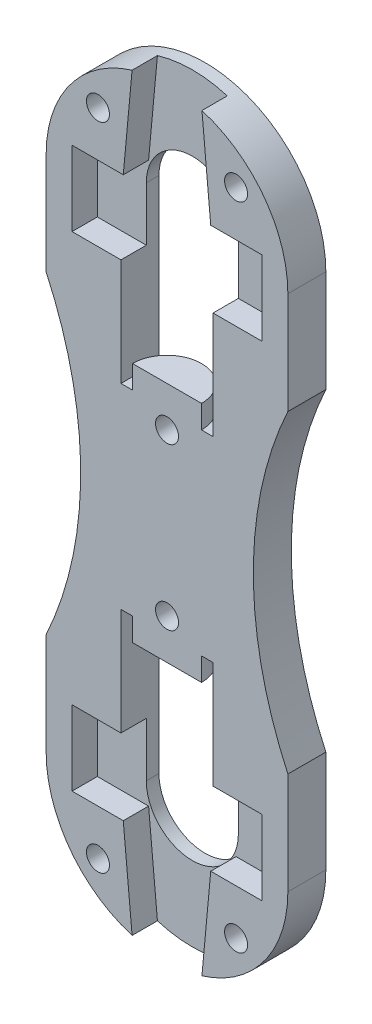
SolidWorks part; units mm, degrees
ref_plane "前视基准面" through (0, 0, 0) normal (0, 0, 1) x (1, 0, 0)
ref_plane "上视基准面" through (0, 0, 0) normal (0, 1, 0) x (1, 0, 0)
ref_plane "右视基准面" through (0, 0, 0) normal (1, 0, 0) x (0, 0, -1)
sketch "草图1" plane through (0, 0, 0) normal (0, 0, 1) x (1, 0, 0)
  line L0 (0, 0) -> (0, 22.5) construction
  line L1 (10.5, -13.6382) -> (10.5, -22.5)
  line L2 (-10.5, 22.5) -> (-10.5, 13.6382)
  line L3 (-4, -22.5) -> (-4, -8.5)
  line L4 (10.5, 22.5) -> (10.5, 13.6382)
  line L5 (-10.5, -13.6382) -> (-10.5, -22.5)
  line L6 (4, -22.5) -> (4, -8.5)
  line L7 (0, 0) -> (40, 0) construction
  line L8 (-4, 22.5) -> (-4, 8.5)
  line L9 (-4, 8.5) -> (4, 8.5)
  line L10 (4, 22.5) -> (4, 8.5)
  line L11 (-4, -8.5) -> (4, -8.5)
  arc A0 (10.5, 22.5) -> (-10.5, 22.5) centre (0, 22.5) ccw
  arc A1 (10.5, -22.5) -> (-10.5, -22.5) centre (0, -22.5) cw
  arc A2 (10.5, 13.6382) -> (10.5, -13.6382) centre (40, 0) ccw
  arc A3 (-10.5, 13.6382) -> (-10.5, -13.6382) centre (-40, 0) cw
  arc A4 (4, 22.5) -> (-4, 22.5) centre (0, 22.5) ccw
  arc A5 (4, -22.5) -> (-4, -22.5) centre (0, -22.5) cw
  circle A6 centre (0, 7) radius 1
  circle A7 centre (0, -7) radius 1
  circle A8 centre (-6, 28.25) radius 1
  circle A9 centre (6, 28.25) radius 1
  circle A10 centre (6, -28.25) radius 1
  circle A11 centre (-6, -28.25) radius 1
  point P0 (0, 0)
  point P15 (0, 26.5)
  point P16 (0, 19.246)
  point P21 (-4, 15.5)
  point P22 (4, 15.5)
  dimension "D3" = 21
  dimension "D2" = 65
  dimension "D6" = 8
  dimension "D9" = 2
  dimension "D11" = 2
  dimension "D1" = 21
  dimension "D4" = 45
  dimension "D5" = 40
  dimension "D7" = 8
  dimension "D8" = 18
  dimension "D10" = 14
  dimension "D12" = 12
  dimension "D13" = 56.5
extrude "凸台-拉伸1" add sketch "草图1" along normal blind 3.3
sketch "草图2" plane through (0, 0, 3.3) normal (0, 0, 1) x (1, 0, 0)
  line L0 (-3.8, 24.3) -> (-2.8714, 34.3)
  line L1 (-8.25, 24.3) -> (-3.8, 24.3)
  line L2 (-8.25, 24.3) -> (-8.25, 17.8)
  line L3 (-8.25, 17.8) -> (8.25, 17.8)
  line L4 (8.25, 24.3) -> (8.25, 17.8)
  line L5 (-8.25, 24.3) -> (8.25, 17.8) construction
  line L6 (-8.25, 17.8) -> (8.25, 24.3) construction
  line L7 (-2.8714, 34.3) -> (2.8714, 34.3)
  line L8 (0, 21.05) -> (0, 34.3) construction
  line L9 (3.8, 24.3) -> (2.8714, 34.3)
  line L10 (3.8, 24.3) -> (8.25, 24.3)
  line L11 (0, 0) -> (16.8737, 0) construction
  line L12 (-10, 4) -> (10, 4) construction
  line L13 (-10, 4) -> (-10, -4) construction
  line L14 (-10, -4) -> (10, -4) construction
  line L15 (10, 4) -> (10, -4) construction
  line L16 (-10, 4) -> (10, -4) construction
  line L17 (-10, -4) -> (10, 4) construction
  line L18 (3.8, -24.3) -> (8.25, -24.3)
  line L19 (8.25, -24.3) -> (8.25, -17.8)
  line L20 (-8.25, -17.8) -> (8.25, -17.8)
  line L21 (-8.25, -24.3) -> (-8.25, -17.8)
  line L22 (-8.25, -24.3) -> (-3.8, -24.3)
  line L23 (-3.8, -24.3) -> (-2.8714, -34.3)
  line L24 (-2.8714, -34.3) -> (2.8714, -34.3)
  line L25 (3.8, -24.3) -> (2.8714, -34.3)
  arc A0 (4, 22.5) -> (-4, 22.5) centre (0, 22.5) ccw construction
  point P0 (0, 21.05)
  point P12 (0, 0)
  dimension "D1" = 6.5
  dimension "D2" = 16.5
  dimension "D3" = 3.8
  dimension "D4" = 10.61
  dimension "D5" = 10
  dimension "D6" = 8
  dimension "D7" = 20
  dimension "D8" = 1.45
extrude "切除-拉伸1" cut sketch "草图2" against normal blind 2.2
sketch "草图3" plane through (0, 8.5, 0) normal (0, 1, 0) x (1, 0, 0)
  line L0 (-4, -3.3) -> (4, -3.3) construction
  line L1 (-3, -3.3) -> (3, -3.3)
  arc A0 (3, -3.3) -> (-3, -3.3) centre (0, -3.3) ccw
  dimension "D1" = 6
extrude "凸台-拉伸2" add sketch "草图3" along normal blind 2
mirror "镜向1" about plane through (0, 0, 0) normal (0, 1, 0) of "凸台-拉伸2"
sketch "草图4" plane through (0, 0, 1.1) normal (0, 0, 1) x (1, 0, 0)
  line L0 (0, 18.5699) -> (0, 24.5699) construction
  line L1 (-4, 18.5699) -> (-4, 24.5699)
  line L2 (4, 18.5699) -> (4, 24.5699)
  line L3 (0, 0) -> (16.5873, 0) construction
  line L4 (0, -18.5699) -> (0, -24.5699) construction
  line L5 (-4, -18.5699) -> (-4, -24.5699)
  line L6 (4, -18.5699) -> (4, -24.5699)
  arc A0 (-4, 18.5699) -> (4, 18.5699) centre (0, 18.5699) ccw
  arc A1 (4, 24.5699) -> (-4, 24.5699) centre (0, 24.5699) ccw
  arc A2 (-4, -18.5699) -> (4, -18.5699) centre (0, -18.5699) cw
  arc A3 (4, -24.5699) -> (-4, -24.5699) centre (0, -24.5699) cw
  point P3 (0, 21.5699)
  point P12 (0, -21.5699)
  dimension "D1" = 4
  dimension "D2" = 3
